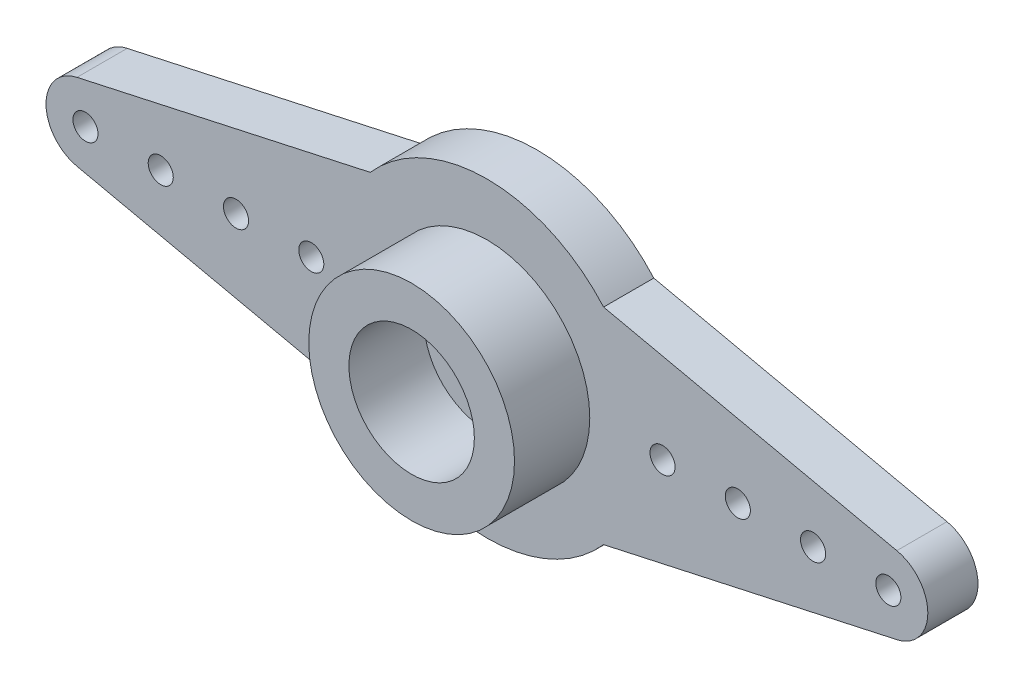
SolidWorks part; units mm, degrees
ref_plane "Front Plane" through (0, 0, 0) normal (0, 0, 1) x (1, 0, 0)
ref_plane "Top Plane" through (0, 0, 0) normal (0, 1, 0) x (1, 0, 0)
ref_plane "Right Plane" through (0, 0, 0) normal (1, 0, 0) x (0, 0, -1)
sketch "Esquisse1" plane through (0, 0, 0) normal (0, 0, 1) x (1, 0, 0)
  line L0 (-16.337, 1.5365) -> (-4.6508, 4.1)
  line L1 (4.6508, 4.1) -> (16.337, 1.5365)
  line L2 (16.337, -1.5365) -> (4.6508, -4.1)
  line L3 (-4.6508, -4.1) -> (-16.337, -1.5365)
  arc A0 (4.6508, 4.1) -> (-4.6508, 4.1) centre (0, 0) ccw
  arc A1 (16.337, -1.5365) -> (16.337, 1.5365) centre (16, 0) ccw
  arc A2 (4.6508, -4.1) -> (-4.6508, -4.1) centre (0, 0) cw
  arc A3 (-16.337, 1.5365) -> (-16.337, -1.5365) centre (-16, 0) ccw
  circle A4 centre (0, 0) radius 1.5
  circle A5 centre (7, 0) radius 0.5
  circle A6 centre (16, 0) radius 0.5
  circle A7 centre (13, 0) radius 0.5
  circle A8 centre (10, 0) radius 0.5
  circle A9 centre (-16, 0) radius 0.5
  circle A10 centre (-13, 0) radius 0.5
  circle A11 centre (-10, 0) radius 0.5
  circle A12 centre (-7, 0) radius 0.5
  dimension "D2" = 6.2
  dimension "D4" = 1.573
  dimension "D5" = 3
  dimension "D6" = 1
  dimension "D1" = 32
  dimension "D3" = 8.2
  dimension "D7" = 7
  dimension "D8" = 3
  dimension "D9" = 3
  dimension "D10" = 7
  dimension "D11" = 10
  dimension "D12" = 3
extrude "Boss.-Extru.1" add sketch "Esquisse1" along normal blind 2
sketch "Esquisse2" plane through (0, 0, 2) normal (0, 0, 1) x (1, 0, 0)
  circle A0 centre (0, 0) radius 4.1
  circle A1 centre (0, 0) radius 2.5
  dimension "D1" = 8.2
  dimension "D2" = 5
extrude "Boss.-Extru.2" add sketch "Esquisse2" along normal blind 3
